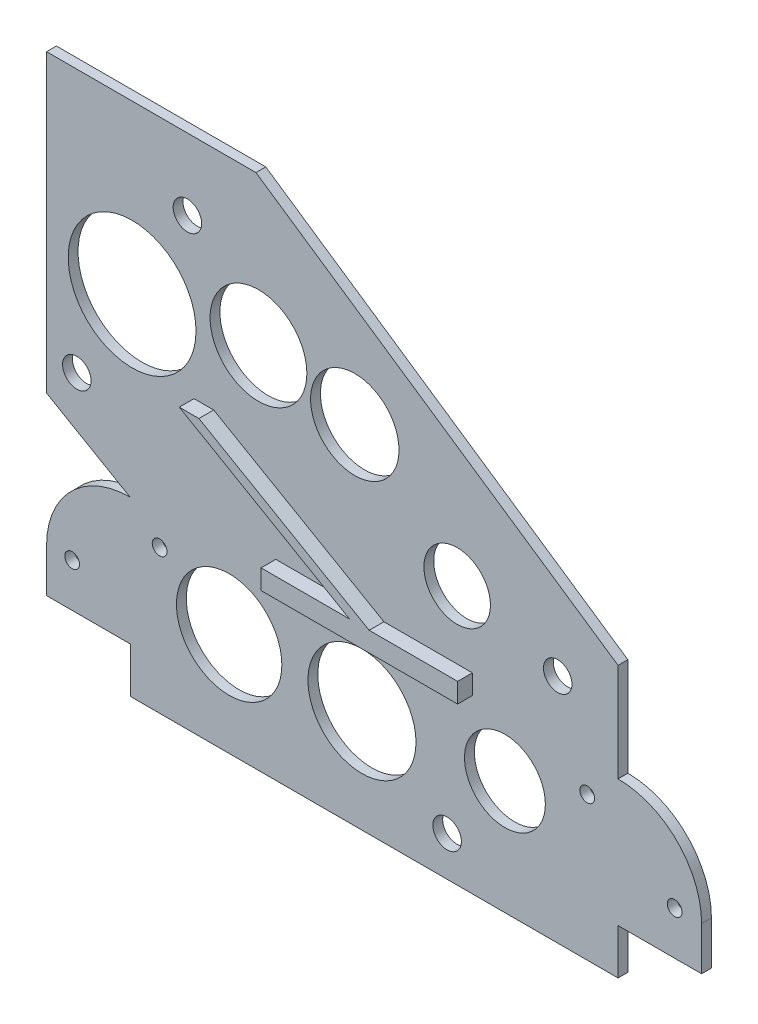
SolidWorks part; units mm, degrees
ref_plane "Front" through (0, 0, 0) normal (0, 0, 1) x (1, 0, 0)
ref_plane "Top" through (0, 0, 0) normal (0, 1, 0) x (1, 0, 0)
ref_plane "Right" through (0, 0, 0) normal (1, 0, 0) x (0, 0, -1)
sketch "草图1" plane through (0, 0, 0) normal (0, 0, 1) x (1, 0, 0)
  line L0 (15, 1.85) -> (15, -8.15) construction
  line L1 (15, -8.15) -> (-60.3442, 35.35) construction
  line L2 (15, -8.15) -> (37.5, 30.8211) construction
  line L3 (-60.3442, 35.35) -> (-37.8442, 74.3211) construction
  line L4 (49.7794, 18.85) -> (49.7794, 38.85)
  line L5 (-49.4505, -16.2369) -> (49.7794, -16.2369)
  line L6 (-66.5, -7) -> (-49.4505, -7)
  line L7 (-66.5, 1.85) -> (-66.5, -7)
  line L8 (-66.5, 88.85) -> (-23.8998, 88.85)
  line L9 (66.7794, 1.85) -> (66.7794, -7)
  line L10 (-49.4505, -7) -> (-49.4505, -16.2369)
  line L11 (66.7794, -7) -> (49.7794, -7)
  line L12 (-66.5, 88.85) -> (-66.5, 28.6845)
  line L13 (49.7794, -7) -> (49.7794, -16.2369)
  line L14 (-60.6108, 25.2648) -> (-66.5, 28.6845)
  line L15 (49.7794, 38.85) -> (-23.8998, 88.85)
  line L16 (0, 13) -> (43.5, 13) construction
  line L17 (43.5, 13) -> (0, 13) construction
  line L18 (0, 1.85) -> (61.3, 1.85) construction
  line L19 (0, 1.85) -> (-61.3, 1.85) construction
  line L20 (-49.5, 18.85) -> (-60.6108, 25.2648)
  line L22 (0, 13) -> (-43.5, 13) construction
  circle A0 centre (-61.3, 1.85) radius 1.5
  circle A1 centre (-43.5, 13) radius 1.5
  circle A2 centre (15, -8.15) radius 2.9
  circle A3 centre (37.5, 30.8211) radius 2.9
  circle A4 centre (-60.3442, 35.35) radius 2.9
  circle A5 centre (-37.8442, 74.3211) radius 2.9
  circle A6 centre (43.5, 13) radius 1.5
  circle A7 centre (61.3, 1.85) radius 1.5
  arc A8 (66.7794, 1.85) -> (49.7794, 18.85) centre (49.7794, 1.85) ccw
  arc A9 (-66.5, 1.85) -> (-49.5, 18.85) centre (-49.5, 1.85) cw
  circle A10 centre (-49.0942, 54.8356) radius 13
  point P14 (-49.4505, -7)
extrude "凸台-拉伸2" add sketch "草图1" along normal blind 2
sketch "草图2" plane through (0, 0, 2) normal (0, 0, 1) x (1, 0, 0)
  line L0 (-1.8603, 22.7136) -> (-36.5013, 42.7136)
  line L1 (2.1397, 22.7136) -> (-32.5013, 42.7136)
  line L2 (-36.5013, 42.7136) -> (-32.5013, 42.7136)
  line L4 (-1.8603, 18.7136) -> (2.1397, 18.7136)
  line L6 (2.1397, 18.7136) -> (20.1397, 18.7136)
  line L7 (20.1397, 18.7136) -> (20.1397, 22.7136)
  line L8 (20.1397, 22.7136) -> (2.1397, 22.7136)
  line L11 (-1.8603, 18.7136) -> (-19.8603, 18.7136)
  line L12 (-19.8603, 18.7136) -> (-19.8603, 22.7136)
  line L13 (-19.8603, 22.7136) -> (-1.8603, 22.7136)
extrude "凸台-拉伸3" add sketch "草图2" along normal blind 3
sketch "草图3" plane through (0, 0, 2) normal (0, 0, 1) x (1, 0, 0)
  circle A0 centre (-23.3849, 58.6342) radius 9.8477
  circle A1 centre (-3.7875, 54.5056) radius 8.9971
  circle A2 centre (-29.3512, 4.7275) radius 10.7213
  circle A3 centre (-2.3257, 4.7275) radius 10.9919
  circle A4 centre (26.762, 6.975) radius 8.2252
  circle A5 centre (17.0409, 36.4756) radius 6.7702
extrude "切除-拉伸1" cut sketch "草图3" against normal through all
